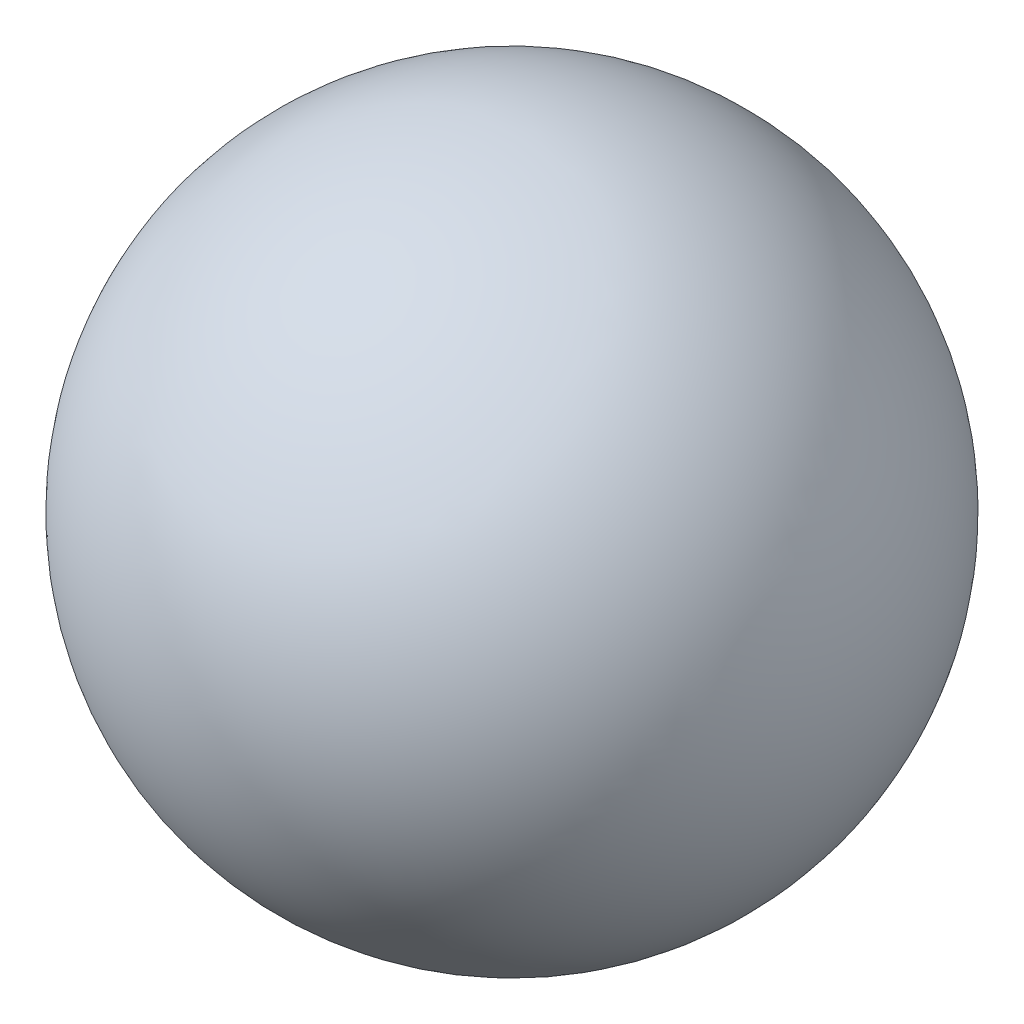
SolidWorks part; units mm, degrees
ref_plane "Front Plane" through (0, 0, 0) normal (0, 0, 1) x (1, 0, 0)
ref_plane "Top Plane" through (0, 0, 0) normal (0, 1, 0) x (1, 0, 0)
ref_plane "Right Plane" through (0, 0, 0) normal (1, 0, 0) x (0, 0, -1)
sketch "Sketch1" plane through (0, 0, 0) normal (0, 0, 1) x (1, 0, 0)
  line L0 (-12, 0) -> (12, 0)
  arc A0 (12, 0) -> (-12, 0) centre (0, 0) cw
  dimension "D1" = 24
revolve "Revolve1" add sketch "Sketch1" angle 360 about L0
scale "Scale1" scale about centroid uniform scaling yes scale factor 1.2
scale "Scale2" scale about centroid uniform scaling yes scale factor 0.1
